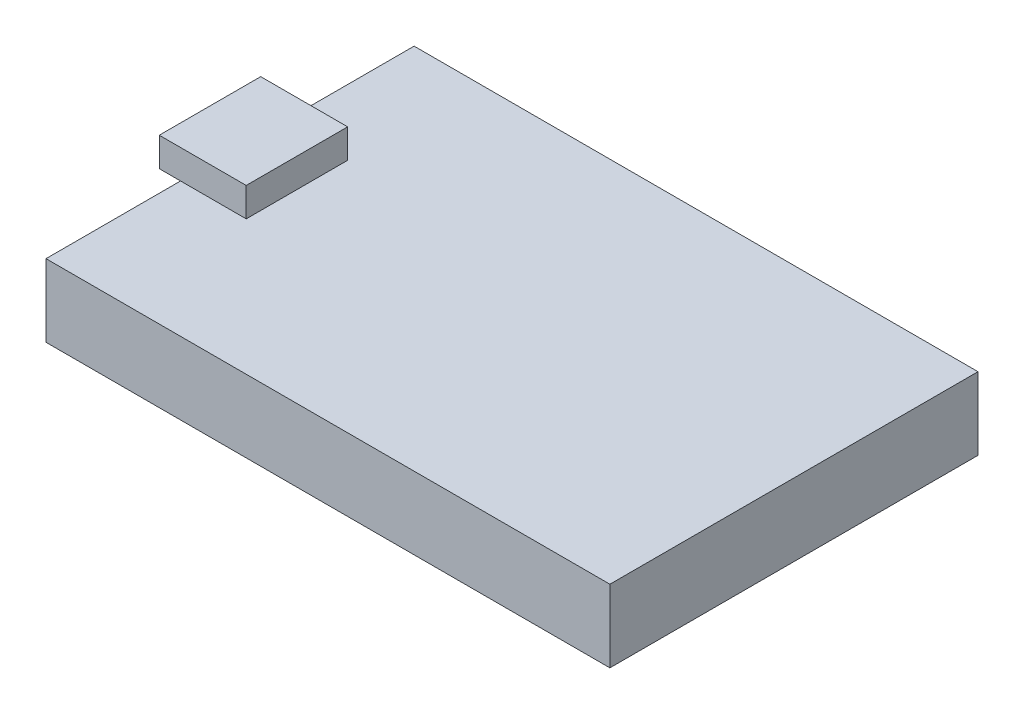
SolidWorks part; units mm, degrees
ref_plane "Front Plane" through (0, 0, 0) normal (0, 0, 1) x (1, 0, 0)
ref_plane "Top Plane" through (0, 0, 0) normal (0, 1, 0) x (1, 0, 0)
ref_plane "Right Plane" through (0, 0, 0) normal (1, 0, 0) x (0, 0, -1)
sketch "Sketch1" plane through (0, 0, 0) normal (0, 1, 0) x (1, 0, 0)
  line L1 (-19.455, -12.7) -> (19.455, -12.7)
  line L2 (-19.455, -12.7) -> (-19.455, 12.7)
  line L3 (-19.455, 12.7) -> (19.455, 12.7)
  line L4 (19.455, -12.7) -> (19.455, 12.7)
  line L5 (-19.455, -12.7) -> (19.455, 12.7) construction
  line L6 (-19.455, 12.7) -> (19.455, -12.7) construction
  point P0 (0, 0)
  dimension "D1" = 38.91
  dimension "D2" = 25.4
extrude "Boss-Extrude1" add sketch "Sketch1" along normal blind 5
sketch "Sketch2" plane through (1.71, 5, 0) normal (0, 1, 0) x (1, 0, 0)
  line L1 (-22.634, -3.416) -> (-16.634, -3.416)
  line L2 (-22.634, -3.416) -> (-22.634, 3.584)
  line L3 (-22.634, 3.584) -> (-16.634, 3.584)
  line L4 (-16.634, -3.416) -> (-16.634, 3.584)
  line L5 (-22.634, -3.416) -> (-16.634, 3.584) construction
  line L6 (-22.634, 3.584) -> (-16.634, -3.416) construction
  point P0 (-19.634, 0.084)
  point P7 (-17.3123, -3.416)
  dimension "D1" = 7
  dimension "D2" = 6
extrude "Boss-Extrude2" add sketch "Sketch2" along normal blind 2
sketch "Sketch4" plane through (0, 5, 0) normal (0, 1, 0) x (1, 0, 0)
  line L0 (-17.4284, 12.7) -> (-17.4284, -12.7)
  line L1 (19.455, 12.7) -> (-19.455, 12.7) construction
  line L2 (-19.455, -12.7) -> (19.455, -12.7) construction
  line L3 (-17.4284, 0) -> (-13.5164, 0)
